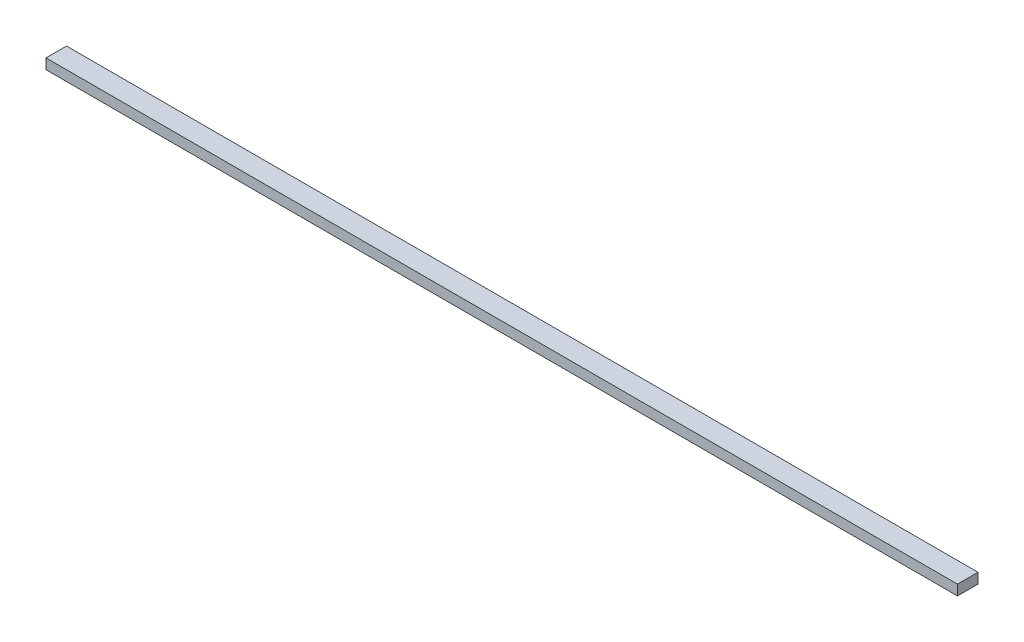
SolidWorks part; units mm, degrees
ref_plane "Front Plane" through (0, 0, 0) normal (0, 0, 1) x (1, 0, 0)
ref_plane "Top Plane" through (0, 0, 0) normal (0, 1, 0) x (1, 0, 0)
ref_plane "Right Plane" through (0, 0, 0) normal (1, 0, 0) x (0, 0, -1)
sketch "Sketch1" plane through (0, 0, 0) normal (0, 1, 0) x (1, 0, 0)
  line L0 (-444.265, 10) -> (444.265, -10) construction
  line L1 (-444.265, 10) -> (444.265, 10)
  line L2 (-444.265, 10) -> (-444.265, -10)
  line L3 (-444.265, -10) -> (444.265, -10)
  line L4 (444.265, 10) -> (444.265, -10)
  dimension "D1" = 888.53
  dimension "D2" = 20
extrude "Boss-Extrude1" add sketch "Sketch1" along normal blind 10
